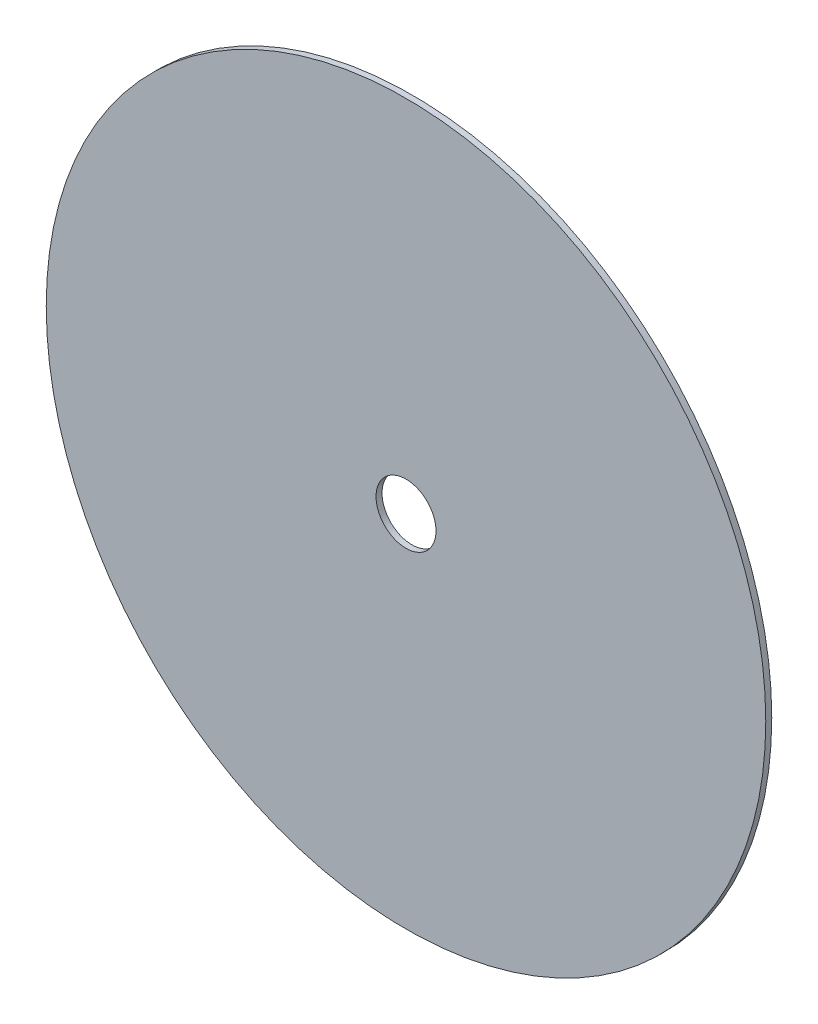
SolidWorks part; units mm, degrees
material "PVC Rigid"
ref_plane "Front Plane" through (0, 0, 0) normal (0, 0, 1) x (1, 0, 0)
ref_plane "Top Plane" through (0, 0, 0) normal (0, 1, 0) x (1, 0, 0)
ref_plane "Right Plane" through (0, 0, 0) normal (1, 0, 0) x (0, 0, -1)
sketch "Sketch1" plane through (0, 0, 0) normal (0, 0, 1) x (1, 0, 0)
  circle A0 centre (0, 0) radius 152.4
  dimension "D1" = 304.8
extrude "Boss-Extrude1" add sketch "Sketch1" along normal blind 2.54
sketch "Sketch2" plane through (0, 0, 2.54) normal (0, 0, 1) x (1, 0, 0)
  circle A0 centre (0, 0) radius 12.7
  dimension "D1" = 25.4
extrude "Cut-Extrude1" cut sketch "Sketch2" against normal through all
